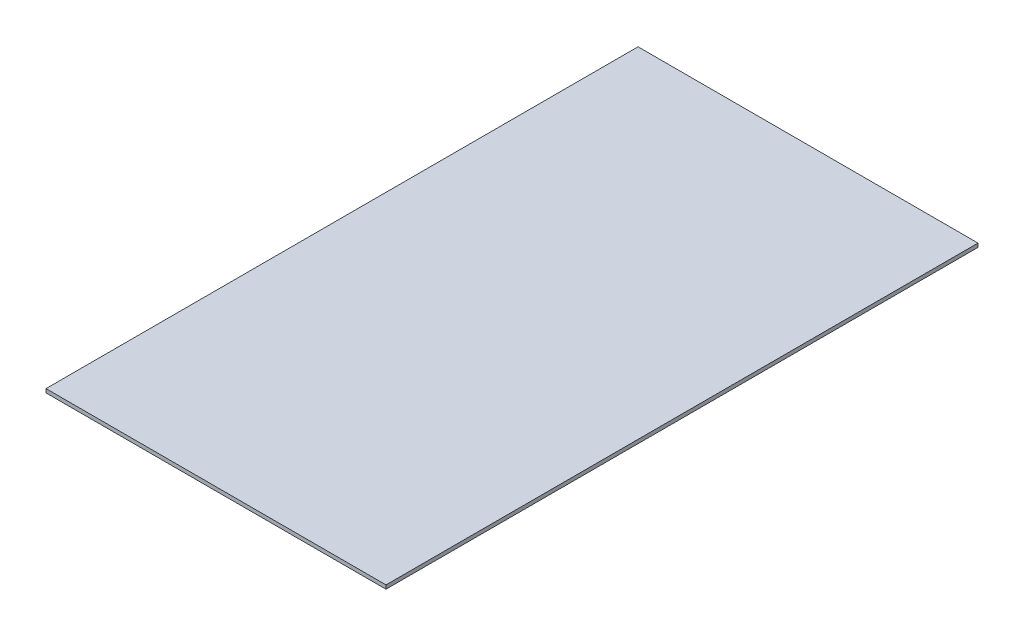
SolidWorks part; units mm, degrees
ref_plane "Front Plane" through (0, 0, 0) normal (0, 0, 1) x (1, 0, 0)
ref_plane "Top Plane" through (0, 0, 0) normal (0, 1, 0) x (1, 0, 0)
ref_plane "Right Plane" through (0, 0, 0) normal (1, 0, 0) x (0, 0, -1)
sketch "Sketch1" plane through (0, 0, 0) normal (0, 1, 0) x (1, 0, 0)
  line L1 (-145, -252.5) -> (145, -252.5)
  line L2 (-145, -252.5) -> (-145, 252.5)
  line L3 (-145, 252.5) -> (145, 252.5)
  line L4 (145, -252.5) -> (145, 252.5)
  line L5 (-145, -252.5) -> (145, 252.5) construction
  line L6 (-145, 252.5) -> (145, -252.5) construction
  point P0 (0, 0)
  dimension "D1" = 505
  dimension "D2" = 290
extrude "Boss-Extrude1" add sketch "Sketch1" along normal blind 3.2
